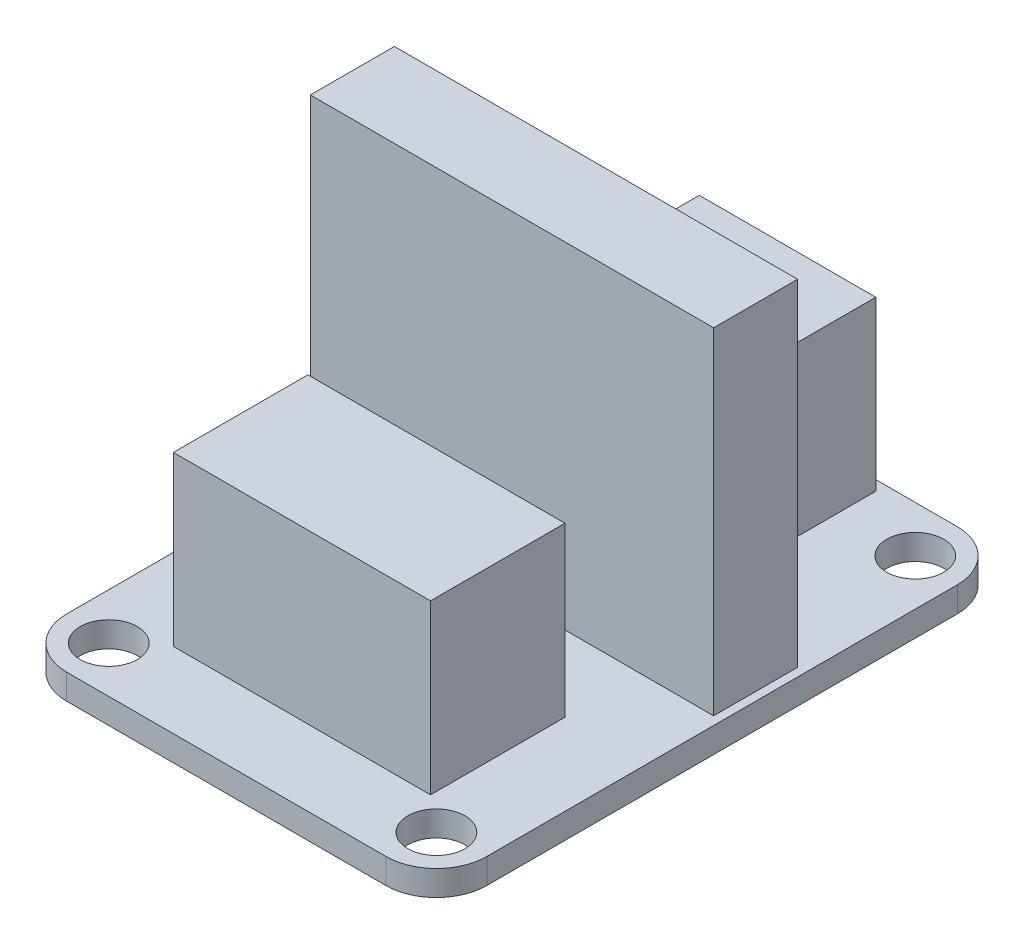
SolidWorks part; units mm, degrees
ref_plane "Ebene vorne" through (0, 0, 0) normal (0, 0, 1) x (1, 0, 0)
ref_plane "Ebene oben" through (0, 0, 0) normal (0, 1, 0) x (1, 0, 0)
ref_plane "Ebene rechts" through (0, 0, 0) normal (1, 0, 0) x (0, 0, -1)
sketch "Skizze2" plane through (0, 0, 0) normal (0, 1, 0) x (1, 0, 0)
  line L1 (-12.5, -17) -> (12.5, -17)
  line L2 (-12.5, -17) -> (-12.5, 17)
  line L3 (-12.5, 17) -> (12.5, 17)
  line L4 (12.5, -17) -> (12.5, 17)
  line L5 (-12.5, -17) -> (12.5, 17) construction
  line L6 (-12.5, 17) -> (12.5, -17) construction
  point P0 (0, 0)
  dimension "D1" = 25
  dimension "D2" = 34
extrude "Aufsatz-Linear austragen1" add sketch "Skizze2" along normal blind 1.5
fillet "Verrundung1" radius 3 4 edges at (-12.5, 0.75, 17) (-12.5, 0.75, -17) (12.5, 0.75, -17) (12.5, 0.75, 17)
hole_wizard "Durchgangsloch für M31" positions "Skizze3" profile "Skizze4" hole size "M3" standard "DIN" end condition through all
sketch "Skizze3" plane through (0, 1.5, 0) normal (0, 1, 0) x (1, 0, 0)
  line L0 (-9.75, -14.25) -> (-9.75, 14.25) construction
  line L1 (-9.75, 14.25) -> (9.75, 14.25) construction
  line L2 (9.75, 14.25) -> (9.75, -14.25) construction
  line L3 (9.75, -14.25) -> (-9.75, -14.25) construction
  line L6 (0, 0) -> (0, 14.25) construction
  line L8 (0, 0) -> (0, -14.25) construction
  point P0 (-9.75, 14.25)
  point P2 (9.75, 14.25)
  point P4 (9.75, -14.25)
  point P6 (-9.75, -14.25)
  dimension "D1" = 19.5
  dimension "D2" = 28.5
sketch "Skizze4" plane through (-9.75, 1.5, -14.25) normal (1, 0, 0) x (0, 0, 1)
  line L0 (0, 0) -> (0, 1.5)
  line L1 (0, 1.5) -> (1.7, 1.5)
  line L2 (1.7, 1.5) -> (1.7, 0)
  line L5 (1.7, 0) -> (0, 0)
  line L11 (0, -6.35) -> (0, 107.95) construction
  dimension "Bohrerdurchmesser" = 3.4
  dimension "Bohrungstiefe" = 1.5
sketch "Skizze5" plane through (0, 1.5, 0) normal (0, 1, 0) x (1, 0, 0)
  line L0 (0, 2.5) -> (0, 0) construction
  line L1 (12, 0) -> (-12, 0)
  line L2 (12, 0) -> (12, 5)
  line L3 (12, 5) -> (-12, 5)
  line L4 (-12, 0) -> (-12, 5)
  line L5 (12, 0) -> (-12, 5) construction
  line L6 (12, 5) -> (-12, 0) construction
  line L7 (9.5, 17) -> (-9.5, 17) construction
  point P0 (0, 2.5)
  dimension "D1" = 24
  dimension "D2" = 5
  dimension "D3" = 12
extrude "Aufsatz-Linear austragen2" add sketch "Skizze5" along normal blind 20
sketch "Skizze6" plane through (0, 1.5, 0) normal (0, 1, 0) x (1, 0, 0)
  line L0 (0, 0) -> (0, 12.4) construction
  line L1 (5.25, 8.4) -> (-5.25, 8.4)
  line L2 (5.25, 8.4) -> (5.25, 16.4)
  line L3 (5.25, 16.4) -> (-5.25, 16.4)
  line L4 (-5.25, 8.4) -> (-5.25, 16.4)
  line L5 (5.25, 8.4) -> (-5.25, 16.4) construction
  line L6 (5.25, 16.4) -> (-5.25, 8.4) construction
  line L7 (9.5, 17) -> (-9.5, 17) construction
  line L8 (-9.5, -17) -> (9.5, -17) construction
  line L9 (7.65, -12.5) -> (-7.65, -12.5)
  line L10 (7.65, -12.5) -> (7.65, -4.5)
  line L11 (7.65, -4.5) -> (-7.65, -4.5)
  line L12 (-7.65, -12.5) -> (-7.65, -4.5)
  line L13 (7.65, -12.5) -> (-7.65, -4.5) construction
  line L14 (7.65, -4.5) -> (-7.65, -12.5) construction
  line L15 (0, -8.5) -> (0, 0) construction
  point P0 (0, 12.4)
  point P10 (0, -8.5)
  dimension "D1" = 10.5
  dimension "D2" = 8
  dimension "D3" = 0.6
  dimension "D4" = 8
  dimension "D5" = 15.3
  dimension "D6" = 4.5
extrude "Aufsatz-Linear austragen3" add sketch "Skizze6" along normal blind 10
